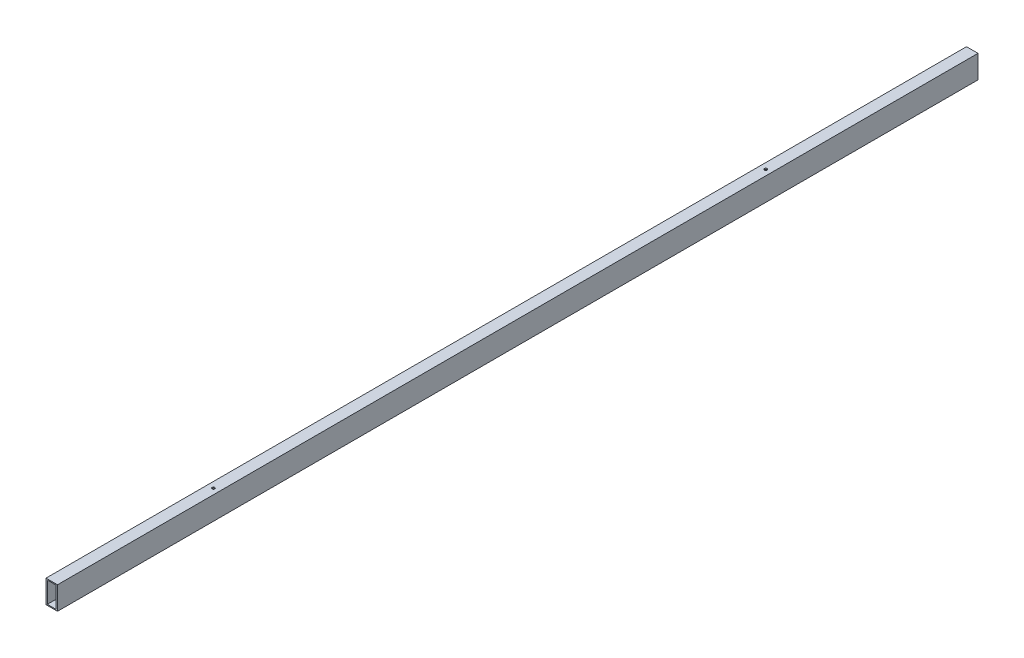
SolidWorks part; units mm, degrees
material "Plastique personnalisé"
ref_plane "Plan de face" through (0, 0, 0) normal (0, 0, 1) x (1, 0, 0)
ref_plane "Plan de dessus" through (0, 0, 0) normal (0, 1, 0) x (1, 0, 0)
ref_plane "Plan de droite" through (0, 0, 0) normal (1, 0, 0) x (0, 0, -1)
sketch "Esquisse1" plane through (0, 0, 0) normal (0, 0, 1) x (1, 0, 0)
  line L1 (-12.5, -25) -> (12.5, -25)
  line L2 (-12.5, -25) -> (-12.5, 25)
  line L3 (-12.5, 25) -> (12.5, 25)
  line L4 (12.5, -25) -> (12.5, 25)
  line L5 (-12.5, -25) -> (12.5, 25) construction
  line L6 (-12.5, 25) -> (12.5, -25) construction
  line L7 (-9.5433, -22.8107) -> (9.5433, -22.8107)
  line L8 (-9.5433, -22.8107) -> (-9.5433, 22.8107)
  line L9 (-9.5433, 22.8107) -> (9.5433, 22.8107)
  line L10 (9.5433, -22.8107) -> (9.5433, 22.8107)
  line L11 (-9.5433, -22.8107) -> (9.5433, 22.8107) construction
  line L12 (-9.5433, 22.8107) -> (9.5433, -22.8107) construction
  point P0 (0, 0)
  point P6 (0, 0)
  dimension "D1" = 50
  dimension "D2" = 25
extrude "Boss.-Extru.1" add sketch "Esquisse1" along normal blind 2000
sketch "Esquisse2" plane through (0, 25, 0) normal (0, 1, 0) x (1, 0, 0)
  circle A0 centre (0.1854, -1648.8727) radius 3
extrude "Enlèv. mat.-Extru.1" cut sketch "Esquisse2" against normal through all both and the other way through all
sketch "Esquisse3" plane through (0, 25, 0) normal (0, 1, 0) x (1, 0, 0)
  circle A0 centre (0.1854, -448.8727) radius 3
extrude "Enlèv. mat.-Extru.2" cut sketch "Esquisse3" against normal through all both and the other way through all
